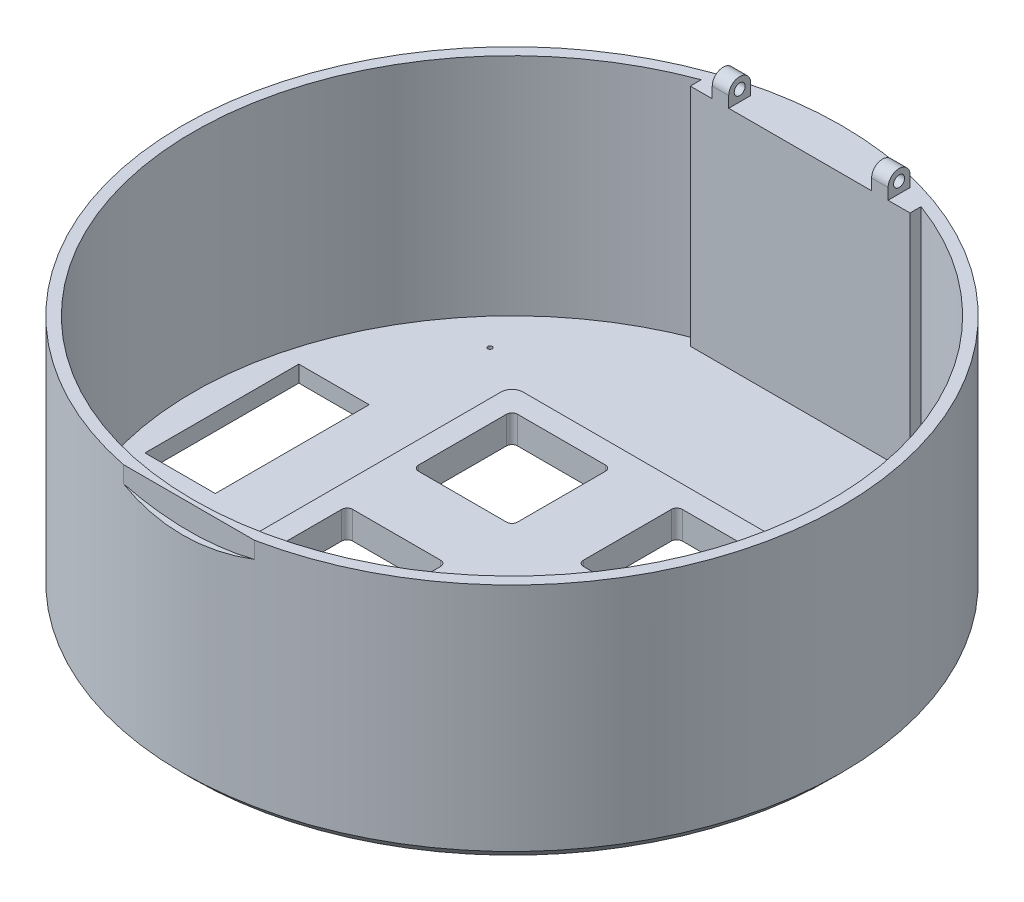
SolidWorks part; units mm, degrees
ref_plane "Front Plane" through (0, 0, 0) normal (0, 0, 1) x (1, 0, 0)
ref_plane "Top Plane" through (0, 0, 0) normal (0, 1, 0) x (1, 0, 0)
ref_plane "Right Plane" through (0, 0, 0) normal (1, 0, 0) x (0, 0, -1)
sketch "Sketch1" plane through (0, 0, 0) normal (0, 1, 0) x (1, 0, 0)
  circle A0 centre (0, 0) radius 15
  dimension "D1" = 30
extrude "Boss-Extrude1" add sketch "Sketch1" along normal blind 11
shell "Shell1" thickness 0.5
sketch "Sketch2" plane through (0, 0, 0) normal (0, -1, 0) x (1, 0, 0)
  line L0 (0, 0) -> (-50000, 0) construction
  line L1 (-6, 6) -> (-1.5, 6)
  line L2 (-6, 6) -> (-6, 1.5)
  line L3 (-6, 1.5) -> (-1.5, 1.5)
  line L4 (-1.5, 6) -> (-1.5, 1.5)
  line L5 (0, 0) -> (0, -50000) construction
  line L6 (0, 0) -> (0, 50000) construction
  line L7 (-1.5, -6) -> (-1.5, -1.5)
  line L8 (-6, -1.5) -> (-1.5, -1.5)
  line L9 (-6, -6) -> (-6, -1.5)
  line L10 (-6, -6) -> (-1.5, -6)
  line L11 (10, 3.5) -> (10, -3.5)
  line L12 (-13.2, 3.5) -> (-10, 3.5)
  line L13 (-13.2, 3.5) -> (-13.2, -3.5)
  line L14 (-13.2, -3.5) -> (-10, -3.5)
  line L15 (-10, 3.5) -> (-10, -3.5)
  line L16 (13.2, -3.5) -> (10, -3.5)
  line L17 (13.2, 3.5) -> (13.2, -3.5)
  line L18 (13.2, 3.5) -> (10, 3.5)
  line L19 (0, 0) -> (50000, 0) construction
  line L20 (6, -6) -> (1.5, -6)
  line L21 (6, -6) -> (6, -1.5)
  line L22 (6, -1.5) -> (1.5, -1.5)
  line L23 (1.5, -6) -> (1.5, -1.5)
  line L24 (1.5, 6) -> (1.5, 1.5)
  line L25 (6, 1.5) -> (1.5, 1.5)
  line L26 (6, 6) -> (6, 1.5)
  line L27 (6, 6) -> (1.5, 6)
  circle A0 centre (-9.5, 8.5) radius 0.1
  circle A1 centre (-9.5, -8.5) radius 0.1
  circle A2 centre (9.5, 8.5) radius 0.1
  circle A3 centre (9.5, -8.5) radius 0.1
  dimension "D8" = 0.2
  dimension "D1" = 4.5
  dimension "D2" = 6
  dimension "D3" = 6
  dimension "D4" = 7
  dimension "D5" = 3.5
  dimension "D6" = 3.2
  dimension "D7" = 4
  dimension "D9" = 3.5
  dimension "D10" = 5
extrude "Cut-Extrude1" cut sketch "Sketch2" against normal up to next
chamfer "Chamfer1" distance 0.5 angle 45 1 edges at (0, 0, 15)
fillet "Fillet1" radius 0.25 16 edges at (1.5, 0.375, -6) (1.5, 0.375, -1.5) (6, 0.375, -6) (6, 0.375, -1.5) (-6, 0.375, -6) (-1.5, 0.375, -6) (-1.5, 0.375, -1.5) (-6, 0.375, -1.5) (-1.5, 0.375, 1.5) (-6, 0.375, 1.5) (-6, 0.375, 6) (-1.5, 0.375, 6) (1.5, 0.375, 1.5) (6, 0.375, 1.5) (6, 0.375, 6) (1.5, 0.375, 6)
sketch "Sketch4" plane through (0, 0, 0) normal (0, 0, 1) x (1, 0, 0)
  line L0 (14.5, 11) -> (-14.5, 11) construction
  line L1 (-3, 11) -> (3, 11)
  line L2 (-3, 11) -> (-3, 10.25)
  line L4 (3, 11) -> (3, 10.25)
  line L5 (0, 0) -> (0, 20.0236) construction
  arc A0 (-3, 10.25) -> (3, 10.25) centre (0, 21.869) ccw
  dimension "D4" = 12
  dimension "D1" = 6
  dimension "D2" = 3
  dimension "D3" = 0.75
extrude "Cut-Extrude2" cut sketch "Sketch4" against normal blind 0.3 from offset 15
sketch "Sketch5" plane through (0, 0.75, 0) normal (0, 1, 0) x (1, 0, 0)
  line L1 (-5, 13.6107) -> (-5, 13.1107)
  line L2 (-5, 13.1107) -> (5, 13.1107)
  line L3 (5, 13.1107) -> (5, 13.6107)
  circle A0 centre (0, 0) radius 14.5 construction
  arc A1 (-5, 13.6107) -> (5, 13.6107) centre (0, 0) cw
  circle A2 centre (0, 0) radius 14.5 construction
  dimension "D1" = 10
  dimension "D2" = 0.5
extrude "Boss-Extrude2" add sketch "Sketch5" along normal up to surface (10.25 mm away) up to face at (0, 11, 14.5)
sketch "Sketch7" plane through (0, 11, 0) normal (0, 1, 0) x (1, 0, 0)
  line L0 (0, 0) -> (0, 26.1334) construction
  line L2 (4, 13.1107) -> (3.25, 13.1107)
  line L3 (4, 13.1107) -> (4, 14.1107)
  line L4 (4, 14.1107) -> (3.25, 14.1107)
  line L5 (3.25, 13.1107) -> (3.25, 14.1107)
  line L6 (5, 13.1107) -> (5, 13.6107) construction
  line L7 (-3.25, 13.1107) -> (-3.25, 14.1107)
  line L8 (-4, 14.1107) -> (-3.25, 14.1107)
  line L9 (-4, 13.1107) -> (-4, 14.1107)
  line L10 (-4, 13.1107) -> (-3.25, 13.1107)
  line L11 (-5, 13.1107) -> (-5, 14.1421) construction
  line L12 (-5, 13.1107) -> (5, 13.1107) construction
  arc A0 (2.985, -14.7) -> (-2.985, -14.7) centre (0, 0) ccw construction
  dimension "D1" = 0.75
  dimension "D2" = 1.75
  dimension "D3" = 1
extrude "Boss-Extrude3" add sketch "Sketch7" along normal blind 1
sketch "Sketch8" plane through (4, 0, 0) normal (1, 0, 0) x (0, 0, -1)
  line L0 (14.1107, 12) -> (14.1107, 11) construction
  line L3 (13.1107, 12) -> (14.1107, 12) construction
  line L4 (13.1107, 11.5) -> (13.1107, 12)
  line L5 (13.1107, 12) -> (14.1107, 12)
  line L6 (14.1107, 12) -> (14.1107, 11.5)
  line L7 (13.1107, 12) -> (13.1107, 11) construction
  arc A0 (13.1107, 11.5) -> (14.1107, 11.5) centre (13.6107, 11.5) cw
  circle A1 centre (13.6107, 11.5) radius 0.25
  line M3 (14.1107, 11) -> (14.1107, 12)
  line M4 (14.1107, 12) -> (13.1107, 12)
  line M5 (13.1107, 12) -> (13.1107, 11)
  dimension "D1" = 0.5
extrude "Cut-Extrude3" cut sketch "Sketch8" against normal through all contours A0 L5 M5 | A0 M4 M3 | A1
sketch "Sketch10" plane through (0, 0.75, 0) normal (0, 1, 0) x (1, 0, 0)
  line L1 (-6.5, 7) -> (6.5, 7)
  line L2 (-7, 6.5) -> (-7, -6.5)
  line L3 (-6.5, -7) -> (6.5, -7)
  line L4 (7, 6.5) -> (7, -6.5)
  line L5 (-7, 7) -> (7, -7) construction
  line L6 (-7, -7) -> (7, 7) construction
  line L12 (-6, 6) -> (6, -6) construction
  line L13 (-6, -6) -> (6, 6) construction
  line L14 (-1.5, -1.75) -> (-1.5, -5.75) construction
  line L15 (-1.75, -6) -> (-5.75, -6) construction
  line L16 (-6, -5.75) -> (-6, -1.75) construction
  line L17 (-5.75, -1.5) -> (-1.75, -1.5) construction
  line L18 (6, -1.75) -> (6, -5.75) construction
  line L19 (5.75, -6) -> (1.75, -6) construction
  line L24 (1.5, -5.75) -> (1.5, -1.75) construction
  line L25 (1.75, -1.5) -> (5.75, -1.5) construction
  line L26 (6, 5.75) -> (6, 1.75) construction
  line L27 (5.75, 1.5) -> (1.75, 1.5) construction
  line L28 (1.5, 1.75) -> (1.5, 5.75) construction
  line L29 (1.75, 6) -> (5.75, 6) construction
  line L30 (-1.5, 5.75) -> (-1.5, 1.75) construction
  line L31 (-1.75, 1.5) -> (-5.75, 1.5) construction
  line L32 (-6, 1.75) -> (-6, 5.75) construction
  line L33 (-5.75, 6) -> (-1.75, 6) construction
  line L34 (-1.5, -1.75) -> (-1.5, -5.75)
  line L35 (-1.75, -6) -> (-5.75, -6)
  line L36 (-6, -5.75) -> (-6, -1.75)
  line L37 (-5.75, -1.5) -> (-1.75, -1.5)
  line L38 (6, -1.75) -> (6, -5.75)
  line L39 (5.75, -6) -> (1.75, -6)
  line L40 (1.5, -5.75) -> (1.5, -1.75)
  line L41 (1.75, -1.5) -> (5.75, -1.5)
  line L42 (6, 5.75) -> (6, 1.75)
  line L43 (5.75, 1.5) -> (1.75, 1.5)
  line L44 (1.5, 1.75) -> (1.5, 5.75)
  line L45 (1.75, 6) -> (5.75, 6)
  line L46 (-1.5, 5.75) -> (-1.5, 1.75)
  line L47 (-1.75, 1.5) -> (-5.75, 1.5)
  line L48 (-6, 1.75) -> (-6, 5.75)
  line L49 (-5.75, 6) -> (-1.75, 6)
  arc A0 (6.5, 7) -> (7, 6.5) centre (6.5, 6.5) cw
  arc A1 (6.5, -7) -> (7, -6.5) centre (6.5, -6.5) ccw
  arc A2 (-7, -6.5) -> (-6.5, -7) centre (-6.5, -6.5) ccw
  arc A3 (-6.5, 7) -> (-7, 6.5) centre (-6.5, 6.5) ccw
  arc A4 (-1.5, -1.75) -> (-1.75, -1.5) centre (-1.75, -1.75) ccw construction
  arc A5 (-1.75, -6) -> (-1.5, -5.75) centre (-1.75, -5.75) ccw construction
  arc A6 (-6, -5.75) -> (-5.75, -6) centre (-5.75, -5.75) ccw construction
  arc A7 (-5.75, -1.5) -> (-6, -1.75) centre (-5.75, -1.75) ccw construction
  arc A8 (6, -1.75) -> (5.75, -1.5) centre (5.75, -1.75) ccw construction
  arc A9 (5.75, -6) -> (6, -5.75) centre (5.75, -5.75) ccw construction
  arc A14 (1.5, -5.75) -> (1.75, -6) centre (1.75, -5.75) ccw construction
  arc A15 (1.75, -1.5) -> (1.5, -1.75) centre (1.75, -1.75) ccw construction
  arc A16 (6, 5.75) -> (5.75, 6) centre (5.75, 5.75) ccw construction
  arc A17 (5.75, 1.5) -> (6, 1.75) centre (5.75, 1.75) ccw construction
  arc A22 (1.5, 1.75) -> (1.75, 1.5) centre (1.75, 1.75) ccw construction
  arc A23 (1.75, 6) -> (1.5, 5.75) centre (1.75, 5.75) ccw construction
  arc A24 (-1.5, 5.75) -> (-1.75, 6) centre (-1.75, 5.75) ccw construction
  arc A25 (-1.75, 1.5) -> (-1.5, 1.75) centre (-1.75, 1.75) ccw construction
  arc A26 (-6, 1.75) -> (-5.75, 1.5) centre (-5.75, 1.75) ccw construction
  arc A27 (-5.75, 6) -> (-6, 5.75) centre (-5.75, 5.75) ccw construction
  arc A28 (-1.5, -1.75) -> (-1.75, -1.5) centre (-1.75, -1.75) ccw
  arc A29 (-1.75, -6) -> (-1.5, -5.75) centre (-1.75, -5.75) ccw
  arc A30 (-6, -5.75) -> (-5.75, -6) centre (-5.75, -5.75) ccw
  arc A31 (-5.75, -1.5) -> (-6, -1.75) centre (-5.75, -1.75) ccw
  arc A32 (6, -1.75) -> (5.75, -1.5) centre (5.75, -1.75) ccw
  arc A33 (5.75, -6) -> (6, -5.75) centre (5.75, -5.75) ccw
  arc A34 (1.5, -5.75) -> (1.75, -6) centre (1.75, -5.75) ccw
  arc A35 (1.75, -1.5) -> (1.5, -1.75) centre (1.75, -1.75) ccw
  arc A36 (6, 5.75) -> (5.75, 6) centre (5.75, 5.75) ccw
  arc A37 (5.75, 1.5) -> (6, 1.75) centre (5.75, 1.75) ccw
  arc A38 (1.5, 1.75) -> (1.75, 1.5) centre (1.75, 1.75) ccw
  arc A39 (1.75, 6) -> (1.5, 5.75) centre (1.75, 5.75) ccw
  arc A40 (-1.5, 5.75) -> (-1.75, 6) centre (-1.75, 5.75) ccw
  arc A41 (-1.75, 1.5) -> (-1.5, 1.75) centre (-1.75, 1.75) ccw
  arc A42 (-6, 1.75) -> (-5.75, 1.5) centre (-5.75, 1.75) ccw
  arc A43 (-5.75, 6) -> (-6, 5.75) centre (-5.75, 5.75) ccw
  point P0 (0, 0)
  point P17 (0, 0)
  dimension "D2" = 0.5
  dimension "D1" = 14
extrude "Boss-Extrude5" add sketch "Sketch10" along normal blind 0.5
mirror "Mirror1" about plane through (0, 0, 0) normal (1, 0, 0) of "Boss-Extrude5"
mirror "Mirror2" about plane through (0, 0, 0) normal (0, 0, 1) of "Boss-Extrude5", "Mirror1"
scale "Scale1" scale about centroid uniform scaling yes scale factor 10
